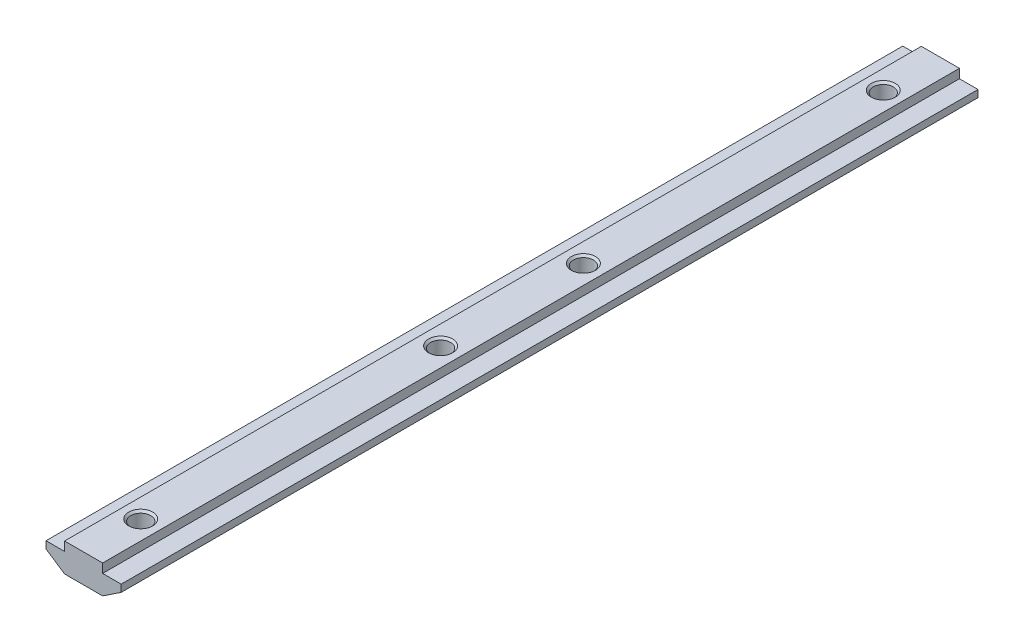
SolidWorks part; units mm, degrees
ref_plane "Спереди" through (0, 0, 0) normal (0, 0, 1) x (1, 0, 0)
ref_plane "Сверху" through (0, 0, 0) normal (0, 1, 0) x (1, 0, 0)
ref_plane "Справа" through (0, 0, 0) normal (1, 0, 0) x (0, 0, -1)
sketch "Эскиз1" plane through (0, 0, 0) normal (0, 0, 1) x (1, 0, 0)
  line L0 (4, 0) -> (-4, 0)
  line L1 (-4, 0) -> (-4, -1.9)
  line L2 (-4, -1.9) -> (-7.9, -1.9)
  line L3 (-7.9, -1.9) -> (-7.9, -3.4)
  line L4 (-7.9, -3.4) -> (-4, -6)
  line L5 (-4, -6) -> (4, -6)
  line L6 (0, -6) -> (0, 0) construction
  line L7 (7.9, -3.4) -> (4, -6)
  line L8 (7.9, -1.9) -> (7.9, -3.4)
  line L9 (4, -1.9) -> (7.9, -1.9)
  line L10 (4, 0) -> (4, -1.9)
  dimension "D1" = 8
  dimension "D2" = 15.8
  dimension "D3" = 6
  dimension "D4" = 4.1
  dimension "D5" = 1.5
extrude "Бобышка-Вытянуть1" add sketch "Эскиз1" along normal mid plane 180
hole_wizard "Отверстие обработанное метчиком M52" positions "Эскиз5" profile "Эскиз6" tap size "M5" standard "ISO" end condition through all
sketch "Эскиз5" plane through (0, 0, 0) normal (0, 1, 0) x (1, 0, 0)
  line L0 (0, 90) -> (0, 78)
  line L1 (4, 90) -> (-4, 90) construction
  line L2 (0, 78) -> (0, 15)
  line L4 (0, -90) -> (0, -78)
  line L5 (4, -90) -> (-4, -90) construction
  line L6 (0, -78) -> (0, -15)
  point P0 (0, 78)
  point P2 (0, 15)
  point P4 (0, -15)
  point P6 (0, -78)
  dimension "D1" = 156
  dimension "D2" = 30
sketch "Эскиз6" plane through (0, 0, -78) normal (1, 0, 0) x (0, 0, 1)
  line L0 (0, 0) -> (0, 6)
  line L1 (0, 6) -> (2.525, 6)
  line L2 (2.1, 5.575) -> (2.1, 0.425)
  line L3 (2.1, 0.425) -> (2.525, 0)
  line L5 (2.525, 0) -> (0, 0)
  line L6 (-2.1, 0.425) -> (-2.525, 0) construction
  line L7 (2.525, 6) -> (2.1, 5.575)
  line L8 (-2.525, 6) -> (-2.1, 5.575) construction
  line L11 (0, -6.35) -> (0, 107.95) construction
  dimension "Диаметр проходного сверла" = 4.2
  dimension "Глубина проходного сверла" = 6
  dimension "Диаметр передней зенковки" = 5.05
  dimension "Угол передней зенковки" = 90
  dimension "Диаметр задней зенковки" = 5.05
  dimension "Угол задней зенковки" = 90
cosmetic thread "Отверстие резьбы5" parameters "D2"=5
cosmetic thread "Отверстие резьбы6" parameters "D2"=5
cosmetic thread "Отверстие резьбы7" parameters "D2"=5
cosmetic thread "Отверстие резьбы8" parameters "D2"=5
